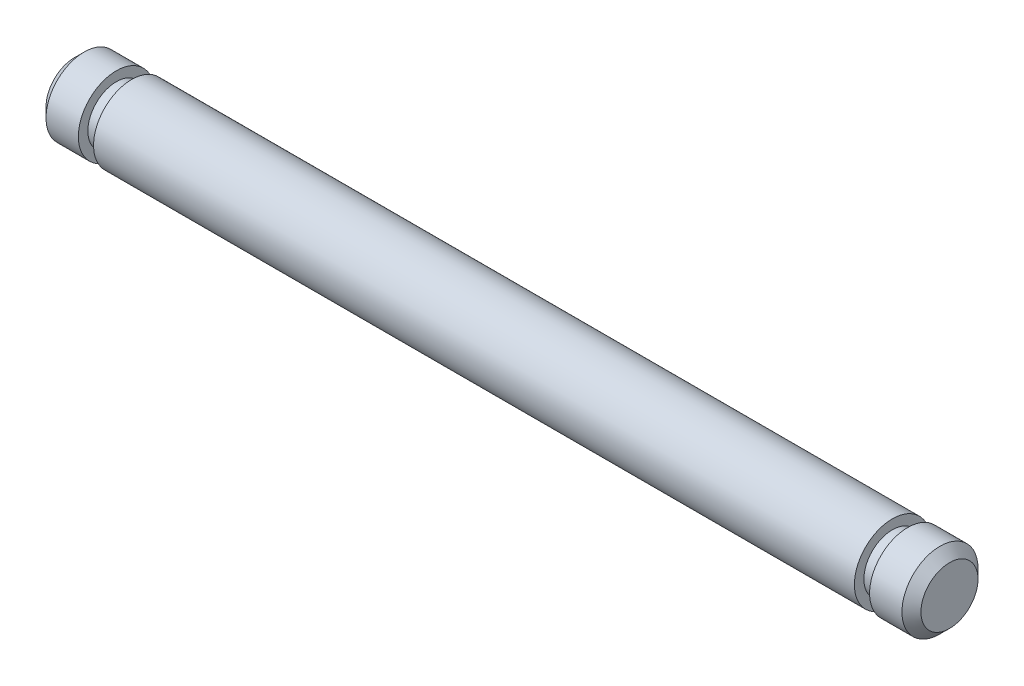
SolidWorks part; units mm, degrees
ref_plane "Front Plane" through (0, 0, 0) normal (0, 0, 1) x (1, 0, 0)
ref_plane "Top Plane" through (0, 0, 0) normal (0, 1, 0) x (1, 0, 0)
ref_plane "Right Plane" through (0, 0, 0) normal (1, 0, 0) x (0, 0, -1)
sketch "Sketch1" plane through (0, 0, 0) normal (1, 0, 0) x (0, 0, -1)
  circle A0 centre (0, 0) radius 2
  dimension "D1" = 4
extrude "Boss-Extrude1" add sketch "Sketch1" along normal mid plane 46
chamfer "Chamfer1" distance 0.5 angle 45 2 edges at (23, 0, -2) (-23, 0, -2)
sketch "Sketch2" plane through (23, 0, 0) normal (1, 0, 0) x (0, 0, -1)
  circle A0 centre (0, 0) radius 2 construction
  circle A1 centre (0, 0) radius 2
  circle A2 centre (0, 0) radius 1.5
  dimension "D1" = 3
extrude "Cut-Extrude1" cut sketch "Sketch2" along normal blind 0.8 from offset 3 offset against normal yes
mirror "Mirror1" about plane through (0, 0, 0) normal (1, 0, 0) of "Cut-Extrude1"
